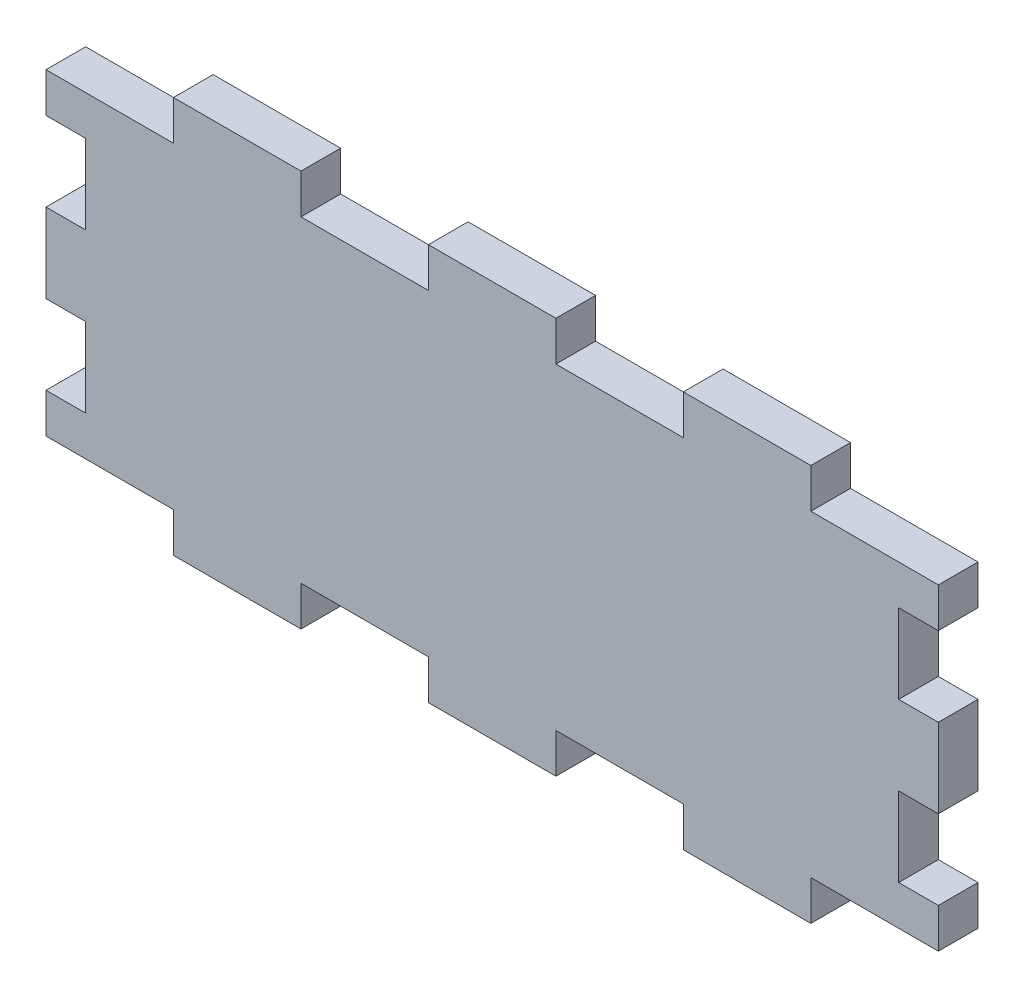
SolidWorks part; units mm, degrees
ref_plane "Front Plane" through (0, 0, 0) normal (0, 0, 1) x (1, 0, 0)
ref_plane "Top Plane" through (0, 0, 0) normal (0, 1, 0) x (1, 0, 0)
ref_plane "Right Plane" through (0, 0, 0) normal (1, 0, 0) x (0, 0, -1)
sketch "Buitenafmeting Rechthoek" plane through (0, 0, 0) normal (0, 0, 1) x (1, 0, 0)
  line L1 (0, 0) -> (90, 0)
  line L2 (0, 0) -> (0, 40)
  line L3 (0, 40) -> (90, 40)
  line L4 (90, 0) -> (90, 40)
  dimension "D1" = 90
  dimension "D2" = 40
extrude "Plaat" add sketch "Buitenafmeting Rechthoek" against normal blind 4
sketch "Tand Hor" plane through (0, 0, 0) normal (0, 0, 1) x (1, 0, 0)
  line L1 (90, 40) -> (0, 40) construction
  line L2 (0, 40) -> (12.8571, 40)
  line L3 (0, 40) -> (0, 36)
  line L4 (0, 36) -> (12.8571, 36)
  line L6 (12.8571, 40) -> (12.8571, 36)
  dimension "D1" = 4
  dimension "D2" = 12.8571
  dimension "D3" = 0
extrude "Tand Boven" cut sketch "Tand Hor" against normal through all
pattern_linear "Tanden Patroon Boven" count 4 spacing 25.7143 along (1, 0, 0) of "Tand Boven"
sketch "Tand Ver" plane through (0, 0, 0) normal (0, 0, 1) x (1, 0, 0)
  line L0 (0, 36) -> (0, 0) construction
  line L1 (0, 32) -> (4, 32)
  line L2 (0, 32) -> (0, 24)
  line L3 (0, 24) -> (4, 24)
  line L4 (4, 32) -> (4, 24)
  dimension "D1" = 4
  dimension "D2" = 8
  dimension "D3" = 32
extrude "Tand Links" cut sketch "Tand Ver" against normal through all
pattern_linear "Tanden Patroon Links" count 2 spacing 16 along (0, -1, 0) of "Tand Links"
sketch "Tand O" plane through (0, 0, 0) normal (0, 0, 1) x (1, 0, 0)
  line L0 (0, 0) -> (90, 0) construction
  line L1 (0, 0) -> (12.8571, 0)
  line L2 (0, 0) -> (0, 4)
  line L3 (0, 4) -> (12.8571, 4)
  line L4 (12.8571, 0) -> (12.8571, 4)
  dimension "D1" = 4
  dimension "D2" = 12.8571
  dimension "D3" = 0
extrude "Tand Onder" cut sketch "Tand O" against normal through all
pattern_linear "Tanden Patroon Onder" count 4 spacing 25.7143 along (1, 0, 0) of "Tand Onder"
sketch "Tand R" plane through (0, 0, 0) normal (0, 0, 1) x (1, 0, 0)
  line L0 (90, 4) -> (90, 36) construction
  line L1 (90, 32) -> (86, 32)
  line L2 (90, 32) -> (90, 24)
  line L3 (90, 24) -> (86, 24)
  line L4 (86, 32) -> (86, 24)
  dimension "D1" = 4
  dimension "D2" = 8
  dimension "D3" = 32
extrude "Tand Rechts" cut sketch "Tand R" against normal through all
pattern_linear "Tanden Patroon Rechts" count 2 spacing 16 along (0, -1, 0) of "Tand Rechts"
equation "\"D1@Buitenafmeting Rechthoek\"= \"Lengte\""
equation "\"D2@Buitenafmeting Rechthoek\" = \"Hoogte\""
equation "\"D1@Plaat\" = \"Dikte\""
equation "\"D3@Tanden Patroon Boven\" = \"LengteHorTand\" * 2"
equation "\"D1@Tanden Patroon Boven\" = \"nPatroonHor\""
equation "\"LengteHorTand\"= \"Lengte\" / \"nHor\"'Spatie tussen verschillende tanden in de lengte"
equation "\"nPatroonHor\"= ( \"nHor\" + 1 ) / 2 - \"GrensHor\"'Aantal kopies van tanden in de lengte"
equation "\"D1@Tand Hor\" = \"Dikte\""
equation "\"D2@Tand Hor\" = \"LengteHorTand\""
equation "\"D1@Tand Ver\" = \"Dikte\""
equation "\"LengteVertTand\"= \"Hoogte\" / \"nVert\"'Spatie tussen verschillende tanden in de hoogte"
equation "\"nPatroonVert\"= ( \"nVert\" + 1 ) / 2 - \"GrensVert\"'Aantal kopies van tanden in de hoogte"
equation "\"D2@Tand Ver\"=\"LengteVertTand\""
equation "\"D3@Tanden Patroon Links\"=\"LengteVertTand\"*2"
equation "\"D3@Tanden Patroon Rechts\"=\"LengteVertTand\"*2"
equation "\"D1@Tanden Patroon Rechts\"=\"nPatroonVert\""
equation "\"D3@Tanden Patroon Onder\"=\"LengteHorTand\"*2"
equation "\"D1@Tanden Patroon Onder\"=\"nPatroonHor\""
equation "\"D1@Tanden Patroon Links\"=\"nPatroonVert\""
equation "\"D3@Tand Ver\"=\"Hoogte\"-\"GrensVert\"*\"LengteVertTand\""
equation "\"D2@Tand R\" = \"LengteVertTand\""
equation "\"D3@Tand R\" = \"Hoogte\" - \"GrensVert\" * \"LengteVertTand\""
equation "\"D2@Tand O\"=\"LengteHorTand\""
equation "\"D3@Tand Hor\"=\"GrensHor\"*\"LengteHorTand\""
equation "\"D3@Tand O\"=\"GrensHor\"*\"LengteHorTand\""
equation "\"Tand Boven\"= IIF ( \"plaatsTandenBoven\" , \"unsuppressed\" , \"suppressed\" )"
equation "\"Tanden Patroon Boven\"= IIF ( \"plaatsTandenBoven\" , \"unsuppressed\" , \"suppressed\" )"
equation "\"Tand Links\"= IIF ( \"plaatsTandenLinks\" , \"unsuppressed\" , \"suppressed\" )"
equation "\"Tanden Patroon Links\"= IIF ( \"plaatsTandenLinks\" , \"unsuppressed\" , \"suppressed\" )"
equation "\"Tand Onder\"= IIF ( \"plaatsTandenOnder\" , \"unsuppressed\" , \"suppressed\" )"
equation "\"Tanden Patroon Onder\"= IIF ( \"plaatsTandenOnder\" , \"unsuppressed\" , \"suppressed\" )"
equation "\"Tand Rechts\"= IIF ( \"plaatsTandenRechts\" , \"unsuppressed\" , \"suppressed\" )"
equation "\"Tanden Patroon Rechts\"= IIF ( \"plaatsTandenRechts\" , \"unsuppressed\" , \"suppressed\" )"
equation "\"D1@Tand O\"=\"Dikte\""
equation "\"D1@Tand R\"=\"Dikte\""
